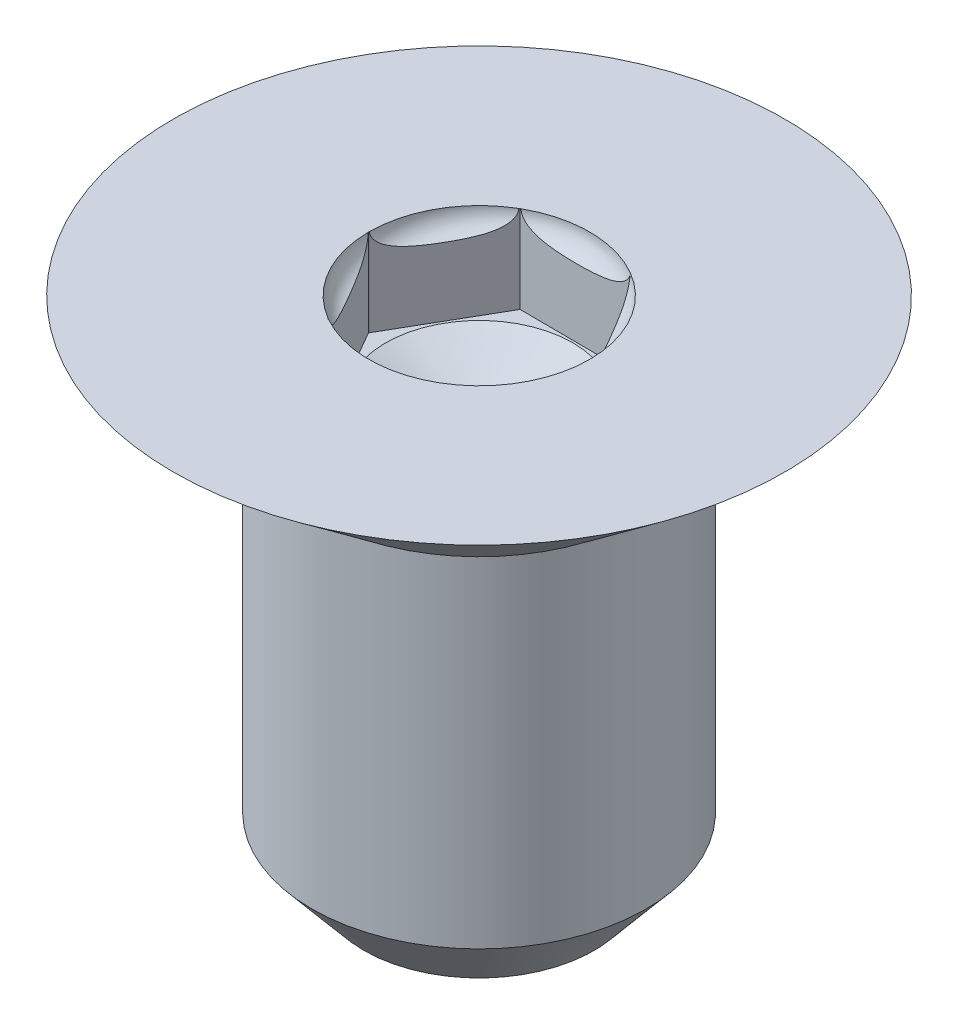
SolidWorks part; units mm, degrees
material "AISI 1020"
ref_plane "Front Plane" through (0, 0, 0) normal (0, 0, 1) x (1, 0, 0)
ref_plane "Top Plane" through (0, 0, 0) normal (0, 1, 0) x (1, 0, 0)
ref_plane "Right Plane" through (0, 0, 0) normal (1, 0, 0) x (0, 0, -1)
sketch "Sketch1" plane through (0, 0, 0) normal (0, 0, 1) x (1, 0, 0)
  line L0 (-9.2326, 23.7881) -> (-9.2326, 5.0412) construction
  line L1 (-9.2326, 19.9898) -> (-5.4226, 19.9898)
  line L2 (-7.1498, 18.6436) -> (-5.4226, 19.9898)
  line L3 (-9.2326, 19.9898) -> (-9.2326, 13.6398)
  line L4 (-9.2326, 13.6398) -> (-7.7973, 13.6398)
  line L5 (-7.1498, 18.6436) -> (-7.1498, 14.4115)
  line L6 (-9.2326, 13.6398) -> (-5.4226, 13.6398) construction
  line L7 (-7.1498, 14.4115) -> (-7.7973, 13.6398)
  dimension "D1" = 6.35
  dimension "D2" = 2.0828
  dimension "D3" = 3.81
  dimension "D7" = 40
revolve "Revolve1" add sketch "Sketch1" angle 360 about L3
sketch "Sketch2" plane through (0, 19.9898, 0) normal (0, 1, 0) x (1, 0, 0)
  line L0 (-9.9266, 1.1938) -> (-8.5481, 1.1938)
  line L1 (-8.5481, 1.1938) -> (-7.8517, 0.0042)
  line L2 (-7.8517, 0.0042) -> (-8.5409, -1.1896)
  line L3 (-8.5409, -1.1896) -> (-9.9194, -1.198)
  line L4 (-9.9194, -1.198) -> (-10.6086, -0.0042)
  line L5 (-10.6086, -0.0042) -> (-9.9266, 1.1938)
extrude "Cut-Extrude1" cut sketch "Sketch2" against normal blind 1.0922
sketch "Sketch4" plane through (0, 19.9898, 0) normal (0, 1, 0) x (1, 0, 0)
  line L0 (-13.8584, 0) -> (-4.1556, 0)
  line L1 (-4.1556, 0) -> (-6.4199, 3.7149)
  line L2 (-6.4199, 3.7149) -> (-9.9225, 4.1925)
  line L3 (-9.9225, 4.1925) -> (-13.7877, 2.7861)
  line L4 (-13.7877, 2.7861) -> (-13.8584, 0)
extrude "Cut-Extrude2" cut sketch "Sketch4" against normal through all
sketch "Sketch5" plane through (0, 0, 0) normal (0, 0, -1) x (-1, 0, 0)
  line L0 (9.2302, 18.8976) -> (9.2302, 19.7025) construction
  line L1 (7.8541, 18.8976) -> (10.6062, 18.8976) construction
  line L3 (9.2302, 18.5293) -> (9.5985, 18.5293)
  line L5 (9.2302, 18.5293) -> (9.2302, 19.9898)
  line L6 (9.2302, 19.9898) -> (10.354, 19.9898)
  line L7 (13.0426, 19.9898) -> (10.6062, 19.9898) construction
  line L8 (9.2302, 18.8976) -> (10.424, 18.8976)
  line L9 (10.397, 18.8976) -> (9.5985, 18.5293)
  line L10 (10.354, 19.9898) -> (10.6062, 19.9898)
  line L11 (10.397, 18.8976) -> (10.397, 19.7412)
  arc A0 (10.397, 19.7412) -> (10.6062, 19.9898) centre (10.354, 19.9898) ccw
revolve "Cut-Revolve1" cut sketch "Sketch5" angle 360 about L0
mirror "Mirror1" about plane through (-13.8584, 13.6398, 0) normal (0, 0, 1) of bodies 105
